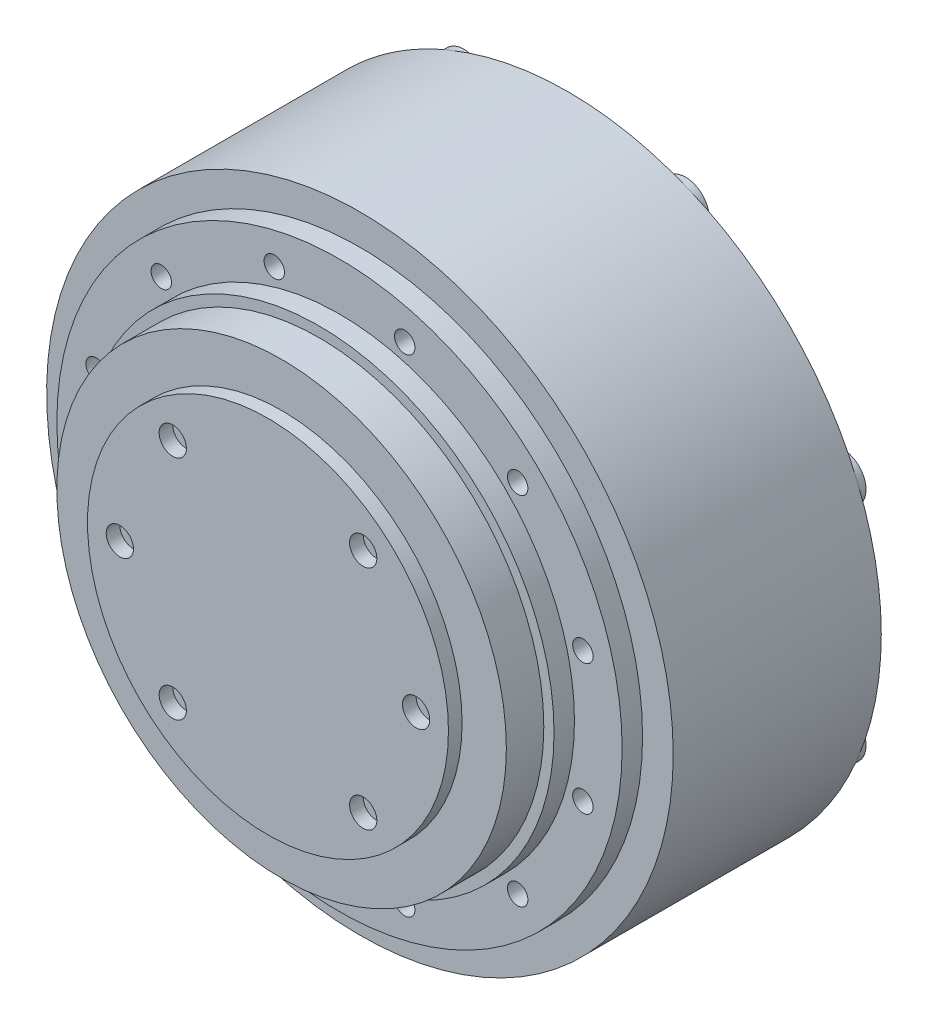
SolidWorks part; units mm, degrees
material "6063-O，挤压棒材(SS)"
ref_plane "前视基准面" through (0, 0, 0) normal (0, 0, 1) x (1, 0, 0)
ref_plane "上视基准面" through (0, 0, 0) normal (0, 1, 0) x (1, 0, 0)
ref_plane "右视基准面" through (0, 0, 0) normal (1, 0, 0) x (0, 0, -1)
other "Configuration Table"
sketch "草图1" plane through (0, 0, 0) normal (0, 0, 1) x (1, 0, 0)
  circle A0 centre (0, 0) radius 46
  dimension "D1" = 92
extrude "凸台-拉伸1" add sketch "草图1" along normal blind 30.55
sketch "草图3" plane through (0, 0, 0) normal (0, 0, -1) x (-1, 0, 0)
  line L0 (17.6034, 42.4985) -> (-17.6034, -42.4985) construction
  line L1 (0, 0) -> (0, 46) construction
  circle A0 centre (0, 0) radius 46 construction
  circle A1 centre (16.264, 39.2649) radius 1.75
  circle A2 centre (16.264, 39.2649) radius 3.5
  circle A3 centre (39.2649, 16.264) radius 1.75
  circle A4 centre (39.2649, 16.264) radius 3.5
  circle A5 centre (39.2649, -16.264) radius 1.75
  circle A6 centre (39.2649, -16.264) radius 3.5
  circle A7 centre (16.264, -39.2649) radius 1.75
  circle A8 centre (16.264, -39.2649) radius 3.5
  circle A9 centre (-16.264, -39.2649) radius 1.75
  circle A10 centre (-16.264, -39.2649) radius 3.5
  circle A11 centre (-39.2649, -16.264) radius 1.75
  circle A12 centre (-39.2649, -16.264) radius 3.5
  circle A13 centre (-39.2649, 16.264) radius 1.75
  circle A14 centre (-39.2649, 16.264) radius 3.5
  circle A15 centre (-16.264, 39.2649) radius 1.75
  circle A16 centre (-16.264, 39.2649) radius 3.5
  point P31 (0, 0)
  dimension "D1" = 7
  dimension "D2" = 3.5
  dimension "D3" = 8
  dimension "D4" = 85
extrude "凸台-拉伸2" add sketch "草图3" along normal blind 1
sketch "草图4" plane through (0, 0, 30.55) normal (0, 0, 1) x (1, 0, 0)
  line L0 (-41.5, 0) -> (41.5, 0) construction
  circle A0 centre (0, 0) radius 41.5
  circle A1 centre (26.163, 26.163) radius 1.5
  circle A2 centre (35.7393, 9.5763) radius 1.5
  circle A3 centre (35.7393, -9.5763) radius 1.5
  circle A4 centre (26.163, -26.163) radius 1.5
  circle A5 centre (9.5763, -35.7393) radius 1.5
  circle A6 centre (-9.5763, -35.7393) radius 1.5
  circle A7 centre (-26.163, -26.163) radius 1.5
  circle A8 centre (-35.7393, -9.5763) radius 1.5
  circle A9 centre (-35.7393, 9.5763) radius 1.5
  circle A10 centre (-26.163, 26.163) radius 1.5
  circle A11 centre (-9.5763, 35.7393) radius 1.5
  circle A12 centre (9.5763, 35.7393) radius 1.5
  point P32 (0, 0)
  dimension "D1" = 83
  dimension "D2" = 3
  dimension "D4" = 74
  dimension "D3" = 12
extrude "凸台-拉伸3" add sketch "草图4" along normal blind 3 contours A0
sketch "草图5" plane through (0, 0, 33.55) normal (0, 0, 1) x (1, 0, 0)
  circle A0 centre (0, 0) radius 33
  dimension "D1" = 66
extrude "凸台-拉伸4" add sketch "草图5" along normal blind 8.5
sketch "草图6" plane through (0, 0, 42.05) normal (0, 0, 1) x (1, 0, 0)
  line L0 (-26.5, 0) -> (26.5, 0) construction
  line L1 (0, 0) -> (0, 21.75) construction
  line L2 (-13.9806, -16.6615) -> (0, 0) construction
  circle A0 centre (0, 0) radius 26.5
  circle A2 centre (-13.9806, -16.6615) radius 2
  circle A12 centre (0, 0) radius 21.75 construction
  circle A13 centre (-21.75, 0) radius 2
  circle A14 centre (-13.9806, 16.6615) radius 2
  circle A15 centre (13.9806, -16.6615) radius 2
  circle A16 centre (21.75, 0) radius 2
  circle A17 centre (13.9806, 16.6615) radius 2
  point P23 (0, 0)
  dimension "D1" = 53
  dimension "D2" = 4
  dimension "D4" = 43.5
  dimension "D3" = 50
extrude "凸台-拉伸5" add sketch "草图6" along normal blind 2
sketch "草图7" plane through (0, 0, 33.55) normal (0, 0, 1) x (1, 0, 0)
  circle A0 centre (0, 0) radius 34.5
  dimension "D1" = 69
extrude "凸台-拉伸6" add sketch "草图7" along normal blind 3
sketch "草图8" plane through (0, 0, 0) normal (0, 0, -1) x (-1, 0, 0)
  line L1 (0, -5) -> (-20, -5)
  line L2 (0, -5) -> (0, 5)
  line L3 (0, 5) -> (-20, 5)
  line L4 (-20, -5) -> (-20, 5)
  line L5 (0, -5) -> (-20, 5) construction
  line L6 (0, 5) -> (-20, -5) construction
  point P4 (-10, 0)
  point P5 (0, 0)
  dimension "D1" = 10
  dimension "D2" = 20
extrude "凸台-拉伸7" add sketch "草图8" along normal blind 5
